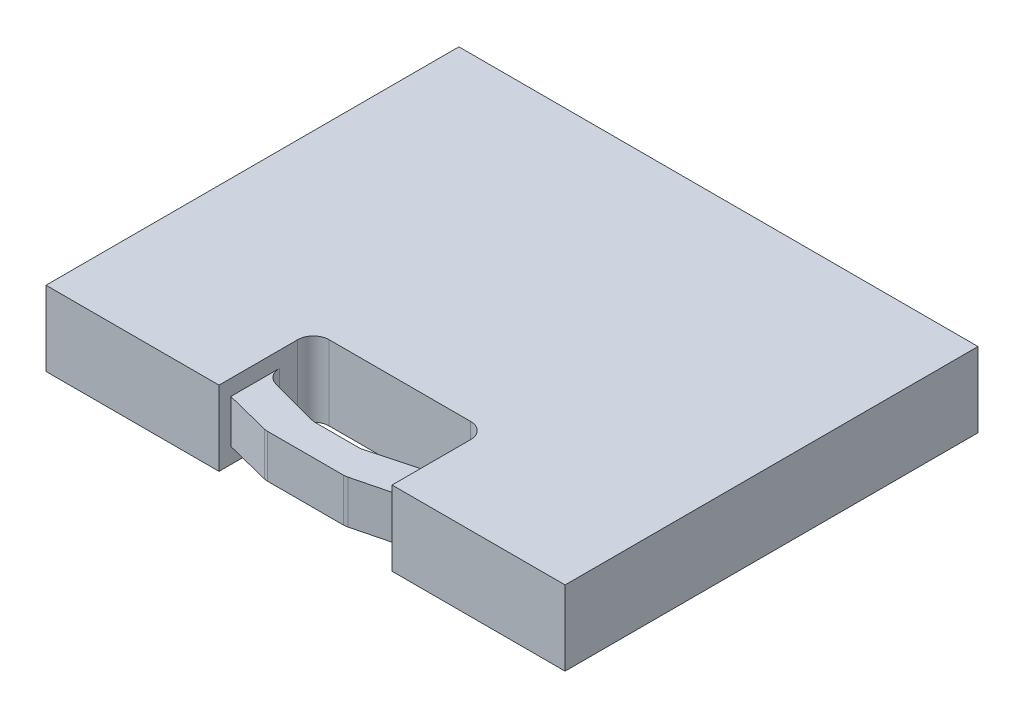
SolidWorks part; units mm, degrees
ref_plane "Front Plane" through (0, 0, 0) normal (0, 0, 1) x (1, 0, 0)
ref_plane "Top Plane" through (0, 0, 0) normal (0, 1, 0) x (1, 0, 0)
ref_plane "Right Plane" through (0, 0, 0) normal (1, 0, 0) x (0, 0, -1)
sketch "Sketch1" plane through (0, 0, 0) normal (0, 1, 0) x (1, 0, 0)
  line L1 (-209.55, -166.6875) -> (209.55, -166.6875)
  line L2 (-209.55, -166.6875) -> (-209.55, 166.6875)
  line L3 (-209.55, 166.6875) -> (209.55, 166.6875)
  line L4 (209.55, -166.6875) -> (209.55, 166.6875)
  line L5 (-209.55, -166.6875) -> (209.55, 166.6875) construction
  line L6 (-209.55, 166.6875) -> (209.55, -166.6875) construction
  point P0 (0, 0)
  dimension "D1" = 333.375
  dimension "D2" = 419.1
extrude "Boss-Extrude1" add sketch "Sketch1" along normal blind 60.325
sketch "Sketch2" plane through (0, 60.325, 0) normal (0, 1, 0) x (1, 0, 0)
  line L0 (0, 0) -> (0, -115.8875) construction
  line L1 (-69.85, -141.2875) -> (69.85, -141.2875)
  line L2 (-69.85, -141.2875) -> (-69.85, -90.4875)
  line L3 (-69.85, -90.4875) -> (69.85, -90.4875)
  line L4 (69.85, -141.2875) -> (69.85, -90.4875)
  line L5 (-69.85, -141.2875) -> (69.85, -90.4875) construction
  line L6 (-69.85, -90.4875) -> (69.85, -141.2875) construction
  line L7 (-209.55, -166.6875) -> (209.55, -166.6875) construction
  line L8 (-69.85, -166.6875) -> (-69.85, -157.1625)
  line L9 (-69.85, -157.1625) -> (-32.169, -166.6875)
  line L10 (-32.169, -166.6875) -> (-69.85, -166.6875)
  line L11 (-69.85, -157.1625) -> (-69.85, -141.2875) construction
  line L12 (0, -166.6875) -> (0, -141.2875) construction
  line L13 (69.85, -157.1625) -> (69.85, -141.2875) construction
  line L14 (32.169, -166.6875) -> (69.85, -166.6875)
  line L15 (69.85, -157.1625) -> (32.169, -166.6875)
  line L16 (69.85, -166.6875) -> (69.85, -157.1625)
  point P0 (0, -115.8875)
  dimension "D1" = 139.7
  dimension "D2" = 50.8
  dimension "D3" = 50.8
  dimension "D4" = 9.525
extrude "Cut-Extrude1" cut sketch "Sketch2" against normal through all
chamfer "Chamfer1" distance 50.8 angle 15 2 edges at (69.85, 30.1625, 141.2875) (-69.85, 30.1625, 141.2875)
fillet "Fillet1" radius 12.7 8 edges at (32.169, 30.1625, 166.6875) (-32.169, 30.1625, 166.6875) (69.85, 30.1625, 127.6757) (19.05, 30.1625, 141.2875) (-19.05, 30.1625, 141.2875) (-69.85, 30.1625, 127.6757) (69.85, 30.1625, 90.4875) (-69.85, 30.1625, 90.4875)
sketch "Sketch3" plane through (0, 60.325, 0) normal (0, 1, 0) x (1, 0, 0)
  line L1 (-69.85, -166.6875) -> (69.85, -166.6875)
  line L2 (-69.85, -166.6875) -> (-69.85, -110.2845)
  line L3 (-69.85, -110.2845) -> (69.85, -110.2845)
  line L4 (69.85, -166.6875) -> (69.85, -110.2845)
extrude "Cut-Extrude2" cut sketch "Sketch3" against normal blind 12.7
sketch "Sketch4" plane through (0, 0, 0) normal (0, -1, 0) x (1, 0, 0)
  line L0 (69.85, 117.9306) -> (69.85, 103.1875) construction
  line L1 (-69.85, 166.6875) -> (69.85, 166.6875)
  line L2 (-69.85, 166.6875) -> (-69.85, 110.5591)
  line L3 (-69.85, 110.5591) -> (69.85, 110.5591)
  line L4 (69.85, 166.6875) -> (69.85, 110.5591)
extrude "Cut-Extrude3" cut sketch "Sketch4" against normal blind 12.7
